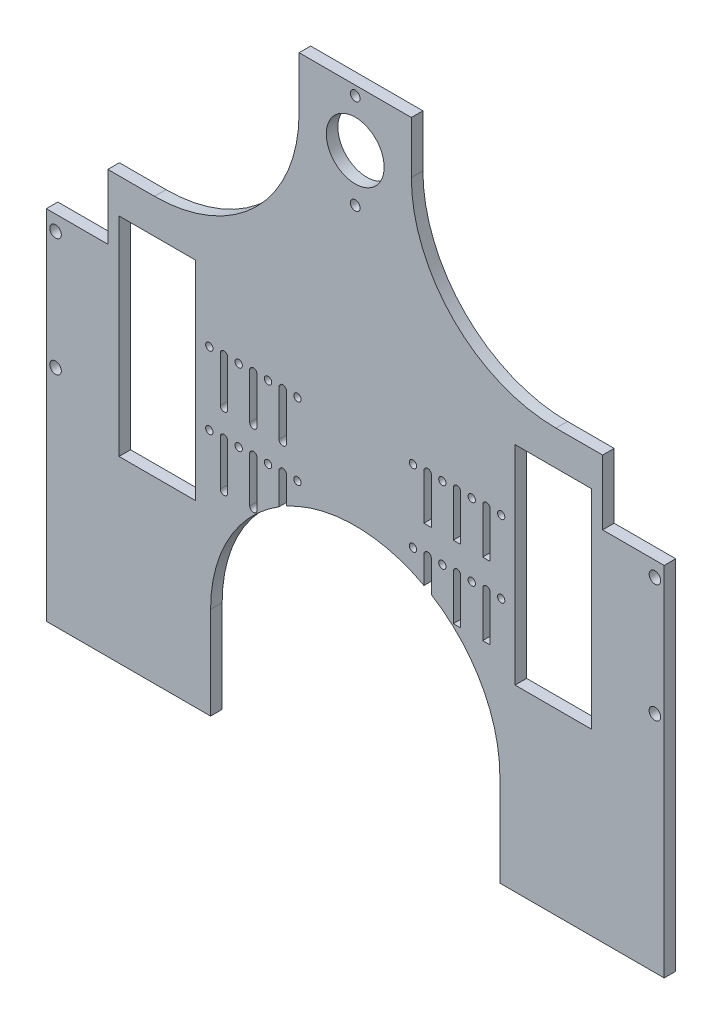
SolidWorks part; units mm, degrees
ref_plane "Front Plane" through (0, 0, 0) normal (0, 0, 1) x (1, 0, 0)
ref_plane "Top Plane" through (0, 0, 0) normal (0, 1, 0) x (1, 0, 0)
ref_plane "Right Plane" through (0, 0, 0) normal (1, 0, 0) x (0, 0, -1)
sketch "Sketch1" plane through (0, 0, 0) normal (0, 0, 1) x (1, 0, 0)
  line L0 (133.5, 0) -> (133.5, -350.4) construction
  line L1 (0, 0) -> (267, 0)
  line L2 (0, 0) -> (0, -350.4)
  line L3 (0, -350.4) -> (267, -350.4)
  line L4 (267, 0) -> (267, -350.4)
  line L9 (202.56, -100) -> (235.56, -100)
  line L10 (202.56, -100) -> (202.56, -190)
  line L11 (202.56, -190) -> (235.56, -190)
  line L12 (235.56, -100) -> (235.56, -190)
  line L13 (196.56, -145) -> (228.95, -145) construction
  line L14 (158.46, -129.375) -> (164.81, -129.375) construction
  line L21 (196.56, -145) -> (235.56, -145) construction
  line L25 (158.46, -160.625) -> (164.81, -160.625) construction
  line L32 (164.81, -129.375) -> (164.81, -134.375) construction
  line L33 (163.2225, -129.375) -> (163.2225, -149.0546)
  line L34 (166.3975, -129.375) -> (166.3975, -149.0546)
  line L35 (177.51, -129.375) -> (177.51, -134.375) construction
  line L36 (175.92, -129.375) -> (175.92, -149.0546)
  line L37 (179.1, -129.375) -> (179.1, -149.0546)
  line L38 (190.21, -129.375) -> (190.21, -134.375) construction
  line L39 (188.62, -129.375) -> (188.62, -149.0546)
  line L40 (191.8, -129.375) -> (191.8, -149.0546)
  line L41 (164.81, -129.375) -> (171.16, -129.375) construction
  line L42 (171.16, -129.375) -> (177.51, -129.375) construction
  line L43 (177.51, -129.375) -> (183.86, -129.375) construction
  line L44 (183.86, -129.375) -> (190.21, -129.375) construction
  line L45 (190.21, -129.375) -> (196.56, -129.375) construction
  line L48 (228.95, -145) -> (164.81, -145) construction
  line L52 (221.56, -100) -> (221.56, -190) construction
  line L53 (211.56, -100) -> (231.56, -100) construction
  line L54 (211.56, -100) -> (211.56, -190) construction
  line L55 (211.56, -190) -> (231.56, -190) construction
  line L56 (231.56, -100) -> (231.56, -190) construction
  line L62 (164.81, -160.625) -> (164.81, -165.625) construction
  line L65 (163.2225, -160.625) -> (163.2225, -180.3046)
  line L68 (166.3975, -160.625) -> (166.3975, -180.3046)
  line L71 (177.51, -160.625) -> (177.51, -165.625) construction
  line L78 (175.92, -160.625) -> (175.92, -180.3046)
  line L79 (179.1, -160.625) -> (179.1, -180.3046)
  line L80 (190.21, -160.625) -> (190.21, -165.625) construction
  line L83 (188.62, -160.625) -> (188.62, -180.3046)
  line L87 (164.81, -145) -> (102.19, -145) construction
  line L90 (196.56, -129.375) -> (196.56, -160.625) construction
  line L93 (164.81, -129.375) -> (164.81, -145) construction
  line L102 (263, -119.5) -> (263, -170.5) construction
  line L103 (235.56, -145) -> (263, -145) construction
  line L105 (191.8, -160.625) -> (191.8, -180.3046)
  line L106 (164.81, -160.625) -> (171.16, -160.625) construction
  line L107 (171.16, -160.625) -> (177.51, -160.625) construction
  line L108 (177.51, -160.625) -> (183.86, -160.625) construction
  line L109 (183.86, -160.625) -> (190.21, -160.625) construction
  line L110 (190.21, -160.625) -> (196.56, -160.625) construction
  line L111 (102.19, -129.375) -> (102.19, -149.0546) construction
  line L112 (103.7775, -129.375) -> (103.7775, -149.0546)
  line L113 (100.6025, -129.375) -> (100.6025, -149.0546)
  line L114 (89.49, -129.375) -> (89.49, -149.0546) construction
  line L115 (91.08, -129.375) -> (91.08, -149.0546)
  line L116 (87.9, -129.375) -> (87.9, -149.0546)
  line L117 (76.79, -129.375) -> (76.79, -149.0546) construction
  line L118 (78.38, -129.375) -> (78.38, -149.0546)
  line L119 (75.2, -129.375) -> (75.2, -149.0546)
  line L120 (102.19, -160.625) -> (102.19, -180.3046) construction
  line L121 (103.7775, -160.625) -> (103.7775, -180.3046)
  line L122 (100.6025, -160.625) -> (100.6025, -180.3046)
  line L123 (89.49, -160.625) -> (89.49, -180.3046) construction
  line L124 (91.08, -160.625) -> (91.08, -180.3046)
  line L125 (87.9, -160.625) -> (87.9, -180.3046)
  line L126 (76.79, -160.625) -> (76.79, -180.3046) construction
  line L127 (78.38, -160.625) -> (78.38, -180.3046)
  line L128 (75.2, -160.625) -> (75.2, -180.3046)
  line L129 (76.79, -160.625) -> (70.44, -160.625) construction
  line L130 (83.14, -160.625) -> (76.79, -160.625) construction
  line L131 (89.49, -160.625) -> (83.14, -160.625) construction
  line L132 (95.84, -160.625) -> (89.49, -160.625) construction
  line L133 (102.19, -160.625) -> (95.84, -160.625) construction
  line L134 (31.44, -145) -> (4, -145) construction
  line L135 (4, -119.5) -> (4, -170.5) construction
  line L136 (102.19, -129.375) -> (102.19, -145) construction
  line L137 (70.44, -129.375) -> (70.44, -160.625) construction
  line L139 (35.44, -100) -> (35.44, -190) construction
  line L140 (55.44, -190) -> (35.44, -190) construction
  line L141 (55.44, -100) -> (55.44, -190) construction
  line L142 (55.44, -100) -> (35.44, -100) construction
  line L143 (45.44, -100) -> (45.44, -190) construction
  line L144 (38.05, -145) -> (102.19, -145) construction
  line L145 (76.79, -129.375) -> (70.44, -129.375) construction
  line L146 (83.14, -129.375) -> (76.79, -129.375) construction
  line L147 (89.49, -129.375) -> (83.14, -129.375) construction
  line L148 (95.84, -129.375) -> (89.49, -129.375) construction
  line L149 (102.19, -129.375) -> (95.84, -129.375) construction
  line L150 (108.54, -160.625) -> (102.19, -160.625) construction
  line L151 (70.44, -145) -> (31.44, -145) construction
  line L152 (108.54, -129.375) -> (102.19, -129.375) construction
  line L153 (70.44, -145) -> (38.05, -145) construction
  line L154 (31.44, -100) -> (31.44, -190)
  line L155 (64.44, -190) -> (31.44, -190)
  line L156 (64.44, -100) -> (64.44, -190)
  line L157 (64.44, -100) -> (31.44, -100)
  arc A6 (191.8, -129.375) -> (188.62, -129.375) centre (190.21, -129.375) cw construction
  arc A7 (188.62, -129.375) -> (191.8, -129.375) centre (190.21, -129.375) cw
  arc A10 (175.92, -129.375) -> (179.1, -129.375) centre (177.51, -129.375) cw
  arc A11 (179.1, -129.375) -> (175.92, -129.375) centre (177.51, -129.375) cw construction
  arc A14 (163.2225, -129.375) -> (166.3975, -129.375) centre (164.81, -129.375) cw
  arc A15 (166.3975, -129.375) -> (163.2225, -129.375) centre (164.81, -129.375) cw construction
  arc A39 (166.3975, -149.0546) -> (163.2225, -149.0546) centre (164.81, -134.375) cw
  circle A40 centre (133.5, -45) radius 2.1
  arc A41 (179.1, -149.0546) -> (175.92, -149.0546) centre (177.51, -134.375) cw
  circle A42 centre (133.5, -4) radius 2.1
  arc A43 (191.8, -149.0546) -> (188.62, -149.0546) centre (190.21, -134.375) cw
  circle A84 centre (263, -119.5) radius 2.5
  circle A85 centre (263, -170.5) radius 2.5
  circle A179 centre (196.56, -129.375) radius 1.59
  arc A182 (191.8, -160.625) -> (188.62, -160.625) centre (190.21, -160.625) cw construction
  arc A183 (188.62, -160.625) -> (191.8, -160.625) centre (190.21, -160.625) cw
  arc A184 (175.92, -160.625) -> (179.1, -160.625) centre (177.51, -160.625) cw
  arc A185 (179.1, -160.625) -> (175.92, -160.625) centre (177.51, -160.625) cw construction
  arc A188 (163.2225, -160.625) -> (166.3975, -160.625) centre (164.81, -160.625) cw
  arc A189 (166.3975, -160.625) -> (163.2225, -160.625) centre (164.81, -160.625) cw construction
  arc A193 (166.3975, -180.3046) -> (163.2225, -180.3046) centre (164.81, -165.625) cw
  arc A195 (179.1, -180.3046) -> (175.92, -180.3046) centre (177.51, -165.625) cw
  arc A197 (191.8, -180.3046) -> (188.62, -180.3046) centre (190.21, -165.625) cw
  circle A198 centre (196.56, -160.625) radius 1.59
  circle A199 centre (133.5, -24.5) radius 12.5
  circle A200 centre (158.46, -129.375) radius 1.59
  circle A201 centre (171.16, -129.375) radius 1.59
  circle A202 centre (183.86, -129.375) radius 1.59
  circle A203 centre (158.46, -160.625) radius 1.59
  circle A204 centre (171.16, -160.625) radius 1.59
  circle A205 centre (183.86, -160.625) radius 1.59
  arc A206 (103.7775, -129.375) -> (100.6025, -129.375) centre (102.19, -129.375) ccw
  arc A207 (100.6025, -149.0546) -> (103.7775, -149.0546) centre (102.19, -149.0546) ccw
  arc A208 (91.08, -129.375) -> (87.9, -129.375) centre (89.49, -129.375) ccw
  arc A209 (87.9, -149.0546) -> (91.08, -149.0546) centre (89.49, -149.0546) ccw
  arc A210 (78.38, -129.375) -> (75.2, -129.375) centre (76.79, -129.375) ccw
  arc A211 (75.2, -149.0546) -> (78.38, -149.0546) centre (76.79, -149.0546) ccw
  arc A212 (103.7775, -160.625) -> (100.6025, -160.625) centre (102.19, -160.625) ccw
  arc A213 (100.6025, -180.3046) -> (103.7775, -180.3046) centre (102.19, -180.3046) ccw
  arc A214 (91.08, -160.625) -> (87.9, -160.625) centre (89.49, -160.625) ccw
  arc A215 (87.9, -180.3046) -> (91.08, -180.3046) centre (89.49, -180.3046) ccw
  arc A216 (78.38, -160.625) -> (75.2, -160.625) centre (76.79, -160.625) ccw
  arc A217 (75.2, -180.3046) -> (78.38, -180.3046) centre (76.79, -180.3046) ccw
  arc A218 (100.6025, -160.625) -> (103.7775, -160.625) centre (102.19, -160.625) ccw construction
  arc A219 (87.9, -160.625) -> (91.08, -160.625) centre (89.49, -160.625) ccw construction
  arc A220 (75.2, -160.625) -> (78.38, -160.625) centre (76.79, -160.625) ccw construction
  arc A221 (100.6025, -129.375) -> (103.7775, -129.375) centre (102.19, -129.375) ccw construction
  arc A222 (87.9, -129.375) -> (91.08, -129.375) centre (89.49, -129.375) ccw construction
  arc A223 (75.2, -129.375) -> (78.38, -129.375) centre (76.79, -129.375) ccw construction
  circle A224 centre (83.14, -160.625) radius 1.59
  circle A225 centre (95.84, -160.625) radius 1.59
  circle A226 centre (108.54, -160.625) radius 1.59
  circle A227 centre (83.14, -129.375) radius 1.59
  circle A228 centre (95.84, -129.375) radius 1.59
  circle A229 centre (108.54, -129.375) radius 1.59
  circle A230 centre (70.44, -160.625) radius 1.59
  circle A234 centre (70.44, -129.375) radius 1.59
  circle A236 centre (4, -170.5) radius 2.5
  circle A237 centre (4, -119.5) radius 2.5
  point P64 (164.81, -145)
  point P65 (102.19, -139.2148)
  point P69 (228.95, -145)
  point P71 (221, -87.34)
  point P76 (233.7, -87.34)
  point P78 (221, -54.5)
  point P82 (233.7, -54.5)
  point P86 (246.4, -54.5)
  point P93 (196.56, -145)
  point P97 (246.4, -87.34)
  point P104 (89.49, -139.2148)
  point P111 (76.79, -139.2148)
  point P119 (102.19, -170.4648)
  point P126 (89.49, -170.4648)
  point P133 (76.79, -170.4648)
  point P155 (133.5, -76.5574)
  point P166 (133.5, -145)
  point P183 (133.5, -76.5574)
  point P199 (70.44, -145)
  point P200 (38.05, -145)
  point P201 (102.19, -145)
  dimension "D5" = 20
  dimension "D10" = 5
  dimension "D12" = 3.18
  dimension "D15" = 5
  dimension "D16" = 5
  dimension "D19" = 3.18
  dimension "D20" = 1.5875
  dimension "D21" = 3.18
  dimension "D22" = 1.59
  dimension "D23" = 3.18
  dimension "D24" = 1.59
  dimension "D25" = 3.18
  dimension "D33" = 3.18
  dimension "D34" = 5
  dimension "D32" = 1.5875
  dimension "D36" = 1.59
  dimension "D37" = 3.18
  dimension "D39" = 1.59
  dimension "D47" = 3.18
  dimension "D49" = 25
  dimension "D53" = 4.2
  dimension "D54" = 4.2
  dimension "D1" = 267
  dimension "D2" = 350.4
  dimension "D3" = 4
  dimension "D4" = 90
  dimension "D6" = 90
  dimension "D7" = 9
  dimension "D8" = 6
  dimension "D9" = 5
  dimension "D11" = 6.35
  dimension "D13" = 6.35
  dimension "D14" = 98.06
  dimension "D17" = 25.5
  dimension "D18" = 4
  dimension "D26" = 5
  dimension "D27" = 6.35
  dimension "D28" = 6.35
  dimension "D29" = 6.35
  dimension "D30" = 6.35
  dimension "D31" = 6.35
  dimension "D38" = 100
  dimension "D40" = 5
  dimension "D41" = 6.35
  dimension "D42" = 6.35
  dimension "D43" = 6.35
  dimension "D44" = 6.35
  dimension "D45" = 6.35
  dimension "D46" = 5
  dimension "D48" = 31.25
  dimension "D52" = 20.5
  dimension "D55" = 4
  dimension "D56" = 20.5
extrude "Boss-Extrude1" add sketch "Sketch1" along normal blind 5
sketch "Sketch12" plane through (0, -350.4, 0) normal (0, -1, 0) x (1, 0, 0)
  line L0 (0, 0) -> (267, 0)
  line L1 (0, 0) -> (0, 5)
  line L2 (267, 0) -> (267, 5)
  line L3 (0, 5) -> (267, 5)
  line L5 (0, 5) -> (267, 5) construction
extrude "Cut-Extrude2" cut sketch "Sketch12" against normal blind 83
sketch "Sketch14" plane through (0, 0, 5) normal (0, 0, 1) x (1, 0, 0)
  line L0 (-135.3499, -267.4) -> (537.3728, -267.4) construction
  line L1 (267, -267.4) -> (0, -267.4) construction
sketch "Sketch11" plane through (0, 0, 5) normal (0, 0, 1) x (1, 0, 0)
  line L1 (0, 0) -> (0, -267.4) construction
  line L2 (267, -267.4) -> (267, 0) construction
  line L3 (0, -95) -> (267, -95) construction
  line L6 (-135.3499, -267.4) -> (537.3728, -267.4) construction
  line L8 (267, 0) -> (0, 0) construction
  line L9 (198.5, 0) -> (198.5, -350.4) construction
  line L10 (262, 0) -> (262, -350.4) construction
  line L11 (193.5, 0) -> (193.5, -350.4) construction
  line L19 (0, -100) -> (267, -100) construction
  line L20 (243.4216, -93.9797) -> (243.4216, -98.9797) construction
  line L22 (133.5, 0) -> (133.5, -350.4) construction
  line L23 (64.44, -100) -> (31.44, -100) construction
  line L27 (179.1, -149.0546) -> (179.1, -129.375) construction
  line L30 (75.2, -129.375) -> (75.2, -149.0546) construction
  line L31 (5, -350.4) -> (5, 0) construction
  line L33 (73.5, -350.4) -> (73.5, 0) construction
  line L34 (-277.981, -404.5615) -> (542.8296, 69.3338) construction
  line L35 (68.5, 0) -> (68.5, -350.4) construction
  line L36 (-309.6509, -284.282) -> (437.3058, 146.9737) construction
  line L37 (384.8254, -173.5315) -> (-153.8253, 137.4586) construction
  line L38 (373.1341, -305.3456) -> (-240.7971, 49.1077) construction
  line L39 (23.5784, -93.9797) -> (23.5784, -98.9797) construction
  line L40 (23.5784, -93.9797) -> (114.787, -15.999) construction
  line L41 (127.279, -30.61) -> (88.1544, 15.1513) construction
  line L42 (243.4216, -93.9797) -> (152.213, -15.999) construction
  line L43 (139.721, -30.61) -> (178.8456, 15.1513) construction
  circle A11 centre (133.5, -227.4) radius 60 construction
  circle A12 centre (133.5, -227.4) radius 62.5 construction
  circle A13 centre (218.12, -146.5661) radius 24.62 construction
  circle A14 centre (91.19, -73.2831) radius 60 construction
  circle A15 centre (133.5, 0) radius 24.62 construction
  circle A17 centre (48.88, -146.5661) radius 24.62 construction
  circle A18 centre (175.81, -73.2831) radius 60 construction
  circle A19 centre (218.12, -267.4) radius 24.62 construction
  circle A20 centre (48.88, -267.4) radius 24.62 construction
  dimension "D4" = 5
  dimension "D5" = 125
  dimension "D3" = 120
  dimension "D9" = 5
  dimension "D10" = 120
  dimension "D11" = 5
  dimension "D12" = 5
  dimension "D13" = 49.24
  dimension "D14" = 5
  dimension "D16" = 49.24
  dimension "D8" = 49.24
  dimension "D15" = 120
  dimension "D6" = 120
  dimension "D2" = 49.24
  dimension "D7" = 5
  dimension "D17" = 40
sketch "Sketch13" plane through (0, 0, 5) normal (0, 0, 1) x (1, 0, 0)
  line L0 (26.6043, -85) -> (220.2496, -85) construction
  line L1 (46.7504, -85) -> (26.6043, -85)
  line L5 (267, 0) -> (267, -113)
  line L6 (0, -100) -> (36, -100) construction
  line L7 (64.44, -100) -> (31.44, -100) construction
  line L8 (0, 0) -> (0, -267.4) construction
  line L9 (-135.3499, -267.4) -> (537.3728, -267.4) construction
  line L10 (267, -267.4) -> (267, 0) construction
  line L12 (71, -227.4) -> (71, -350.4)
  line L14 (71, -350.4) -> (196, -350.4)
  line L15 (196, -227.4) -> (196, -350.4)
  line L16 (267, 0) -> (161.9401, 0)
  line L17 (68.5, 0) -> (68.5, -350.4) construction
  line L20 (105.0599, 0) -> (0, 0)
  line L21 (267, 0) -> (0, 0) construction
  line L31 (240.3957, -85) -> (240.3957, -113)
  line L32 (267, -113) -> (240.3957, -113)
  line L33 (220.2496, -85) -> (240.3957, -85)
  line L35 (133.5, 0) -> (133.5, -350.4) construction
  line L36 (0, -113) -> (26.6043, -113)
  line L37 (26.6043, -85) -> (26.6043, -113)
  line L38 (0, 0) -> (0, -113)
  arc A0 (46.7504, -85) -> (105.0599, 0) centre (46.7504, -22.5) ccw
  arc A1 (161.9401, 0) -> (220.2496, -85) centre (220.2496, -22.5) ccw
  circle A2 centre (46.7504, -22.5) radius 65 construction
  arc A3 (267, -67.6597) -> (240.3957, -84.2992) centre (220.2496, -22.5) ccw construction
  circle A4 centre (133.5, 0) radius 24.62 construction
  arc A5 (196, -227.4) -> (71, -227.4) centre (133.5, -227.4) ccw
  circle A6 centre (133.5, -227.4) radius 62.5 construction
  dimension "D2" = 130
  dimension "D3" = 62.5
  dimension "D4" = 130
  dimension "D5" = 62.5
  dimension "D1" = 15
  dimension "D6" = 154.4
  dimension "D8" = 26.6043
extrude "Cut-Extrude3" cut sketch "Sketch13" against normal through all
sketch "Sketch15" plane through (0, 0, 5) normal (0, 0, 1) x (1, 0, 0)
  line L0 (157.7496, 13.1038) -> (157.7496, -22.5) construction
  line L1 (109.2504, 16.9922) -> (109.2504, -22.5) construction
  line L2 (161.9401, 0) -> (105.0599, 0) construction
  line L3 (109.2504, -22.5) -> (109.2504, 0)
  line L4 (109.2504, -22.5) -> (80.4559, -22.5)
  line L5 (109.2504, 0) -> (80.4559, 0)
  line L6 (80.4559, -22.5) -> (80.4559, 0)
  line L7 (157.7496, -22.5) -> (157.7496, 0)
  line L8 (157.7496, -22.5) -> (165.496, -22.5)
  line L9 (157.7496, 0) -> (165.496, 0)
  line L10 (165.496, -22.5) -> (165.496, 0)
  arc A0 (46.7504, -85) -> (105.0599, 0) centre (46.7504, -22.5) ccw construction
  arc A1 (161.9401, 0) -> (220.2496, -85) centre (220.2496, -22.5) ccw construction
extrude "Cut-Extrude4" cut sketch "Sketch15" against normal blind 10
